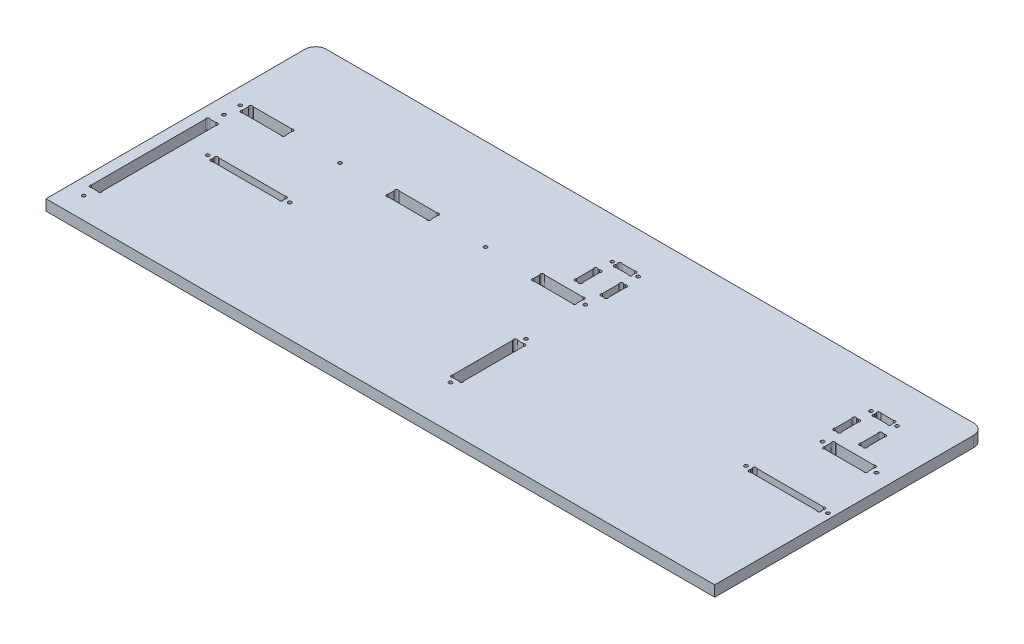
SolidWorks part; units mm, degrees
ref_plane "Plan de face" through (0, 0, 0) normal (0, 0, 1) x (1, 0, 0)
ref_plane "Plan de dessus" through (0, 0, 0) normal (0, 1, 0) x (1, 0, 0)
ref_plane "Plan de droite" through (0, 0, 0) normal (1, 0, 0) x (0, 0, -1)
sketch "Esquisse1" plane through (0, 0, 0) normal (0, 1, 0) x (1, 0, 0)
  line L26 (317, 211.2627) -> (317, 212.7373)
  line L28 (319.2627, 215) -> (330.7373, 215)
  line L29 (333, 211.2627) -> (333, 212.7373)
  line L30 (330.7373, 209) -> (319.2627, 209)
  line L31 (312.2627, 179.5) -> (313.7373, 179.5)
  line L32 (312.2627, 199.5) -> (313.7373, 199.5)
  line L33 (310, 197.2373) -> (310, 181.7627)
  line L34 (316, 181.7627) -> (316, 197.2373)
  line L35 (334, 181.7627) -> (334, 197.2373)
  line L36 (340, 197.2373) -> (340, 181.7627)
  line L37 (337.7373, 199.5) -> (336.2627, 199.5)
  line L38 (337.7373, 179.5) -> (336.2627, 179.5)
  line L39 (552.2627, 179.5) -> (553.7373, 179.5)
  line L40 (552.2627, 199.5) -> (553.7373, 199.5)
  line L41 (550, 197.2373) -> (550, 181.7627)
  line L42 (556, 181.7627) -> (556, 197.2373)
  line L43 (574, 181.7627) -> (574, 197.2373)
  line L44 (580, 197.2373) -> (580, 181.7627)
  line L45 (577.7373, 199.5) -> (576.2627, 199.5)
  line L46 (577.7373, 179.5) -> (576.2627, 179.5)
  line L47 (559.2627, 209) -> (570.7373, 209)
  line L48 (557, 211.2627) -> (557, 212.7373)
  line L49 (570.7373, 215) -> (559.2627, 215)
  line L50 (573, 211.2627) -> (573, 212.7373)
  line L55 (560, 167.7373) -> (560, 162.2627)
  line L56 (600, 167.7373) -> (600, 162.2627)
  line L57 (562.2627, 170) -> (597.7373, 170)
  line L58 (597.7373, 160) -> (562.2627, 160)
  line L59 (292.2627, 160) -> (327.7373, 160)
  line L60 (327.7373, 170) -> (292.2627, 170)
  line L61 (290, 167.7373) -> (290, 162.2627)
  line L62 (330, 167.7373) -> (330, 162.2627)
  line L64 (20, 167.7373) -> (20, 162.2627)
  line L65 (60, 167.7373) -> (60, 162.2627)
  line L66 (22.2627, 170) -> (57.7373, 170)
  line L67 (57.7373, 160) -> (22.2627, 160)
  line L70 (155, 167.7373) -> (155, 162.2627)
  line L71 (195, 167.7373) -> (195, 162.2627)
  line L72 (157.2627, 170) -> (192.7373, 170)
  line L73 (192.7373, 160) -> (157.2627, 160)
  line L76 (10, 250) -> (610, 250)
  line L77 (0, 240) -> (0, 0)
  line L78 (0, 0) -> (620, 0)
  line L79 (620, 240) -> (620, 0)
  line L84 (12.2627, 30) -> (17.7373, 30)
  line L85 (12.2627, 140) -> (17.7373, 140)
  line L86 (10, 137.7373) -> (10, 32.2627)
  line L87 (20, 32.2627) -> (20, 137.7373)
  line L98 (337.7373, 45) -> (332.2627, 45)
  line L99 (337.7373, 105) -> (332.2627, 105)
  line L100 (340, 47.2627) -> (340, 102.7373)
  line L101 (330, 102.7373) -> (330, 47.2627)
  line L109 (610, 109.2627) -> (610, 110.7373)
  line L110 (544, 109.2627) -> (544, 110.7373)
  line L111 (607.7373, 107) -> (546.2627, 107)
  line L112 (546.2627, 113) -> (607.7373, 113)
  line L113 (108.7373, 113) -> (47.2627, 113)
  line L114 (47.2627, 107) -> (108.7373, 107)
  line L115 (111, 109.2627) -> (111, 110.7373)
  line L116 (45, 109.2627) -> (45, 110.7373)
  arc A0 (319.2627, 215) -> (317, 212.7373) centre (318.1314, 213.8686) ccw
  arc A1 (319.2627, 209) -> (317, 211.2627) centre (318.1314, 210.1314) cw
  arc A2 (330.7373, 209) -> (333, 211.2627) centre (331.8686, 210.1314) ccw
  arc A3 (330.7373, 215) -> (333, 212.7373) centre (331.8686, 213.8686) cw
  arc A4 (313.7373, 179.5) -> (316, 181.7627) centre (314.8686, 180.6314) ccw
  arc A5 (312.2627, 179.5) -> (310, 181.7627) centre (311.1314, 180.6314) cw
  arc A6 (312.2627, 199.5) -> (310, 197.2373) centre (311.1314, 198.3686) ccw
  arc A7 (313.7373, 199.5) -> (316, 197.2373) centre (314.8686, 198.3686) cw
  arc A8 (336.2627, 179.5) -> (334, 181.7627) centre (335.1314, 180.6314) cw
  arc A9 (336.2627, 199.5) -> (334, 197.2373) centre (335.1314, 198.3686) ccw
  arc A10 (337.7373, 199.5) -> (340, 197.2373) centre (338.8686, 198.3686) cw
  arc A11 (337.7373, 179.5) -> (340, 181.7627) centre (338.8686, 180.6314) ccw
  arc A12 (552.2627, 179.5) -> (550, 181.7627) centre (551.1314, 180.6314) cw
  arc A13 (552.2627, 199.5) -> (550, 197.2373) centre (551.1314, 198.3686) ccw
  arc A14 (553.7373, 199.5) -> (556, 197.2373) centre (554.8686, 198.3686) cw
  arc A15 (553.7373, 179.5) -> (556, 181.7627) centre (554.8686, 180.6314) ccw
  arc A16 (576.2627, 199.5) -> (574, 197.2373) centre (575.1314, 198.3686) ccw
  arc A17 (577.7373, 199.5) -> (580, 197.2373) centre (578.8686, 198.3686) cw
  arc A18 (577.7373, 179.5) -> (580, 181.7627) centre (578.8686, 180.6314) ccw
  arc A19 (576.2627, 179.5) -> (574, 181.7627) centre (575.1314, 180.6314) cw
  arc A20 (559.2627, 215) -> (557, 212.7373) centre (558.1314, 213.8686) ccw
  arc A21 (559.2627, 209) -> (557, 211.2627) centre (558.1314, 210.1314) cw
  arc A22 (570.7373, 209) -> (573, 211.2627) centre (571.8686, 210.1314) ccw
  arc A23 (570.7373, 215) -> (573, 212.7373) centre (571.8686, 213.8686) cw
  circle A24 centre (313, 212) radius 1.6
  circle A25 centre (337, 212) radius 1.6
  circle A26 centre (553, 212) radius 1.6
  circle A27 centre (577, 212) radius 1.6
  circle A28 centre (555, 165) radius 1.6
  arc A29 (560, 162.2627) -> (562.2627, 160) centre (561.1314, 161.1314) ccw
  arc A30 (560, 167.7373) -> (562.2627, 170) centre (561.1314, 168.8686) cw
  arc A31 (600, 167.7373) -> (597.7373, 170) centre (598.8686, 168.8686) ccw
  arc A32 (600, 162.2627) -> (597.7373, 160) centre (598.8686, 161.1314) cw
  circle A33 centre (605, 165) radius 1.6
  arc A34 (290, 162.2627) -> (292.2627, 160) centre (291.1314, 161.1314) ccw
  arc A35 (290, 167.7373) -> (292.2627, 170) centre (291.1314, 168.8686) cw
  arc A36 (330, 167.7373) -> (327.7373, 170) centre (328.8686, 168.8686) ccw
  arc A37 (330, 162.2627) -> (327.7373, 160) centre (328.8686, 161.1314) cw
  circle A38 centre (335, 165) radius 1.6
  circle A39 centre (15, 165) radius 1.6
  arc A40 (20, 162.2627) -> (22.2627, 160) centre (21.1314, 161.1314) ccw
  arc A41 (20, 167.7373) -> (22.2627, 170) centre (21.1314, 168.8686) cw
  arc A42 (60, 167.7373) -> (57.7373, 170) centre (58.8686, 168.8686) ccw
  arc A43 (60, 162.2627) -> (57.7373, 160) centre (58.8686, 161.1314) cw
  arc A44 (155, 162.2627) -> (157.2627, 160) centre (156.1314, 161.1314) ccw
  arc A45 (155, 167.7373) -> (157.2627, 170) centre (156.1314, 168.8686) cw
  arc A46 (195, 162.2627) -> (192.7373, 160) centre (193.8686, 161.1314) cw
  arc A47 (195, 167.7373) -> (192.7373, 170) centre (193.8686, 168.8686) ccw
  circle A48 centre (242.5, 165) radius 1.6
  circle A49 centre (107.5, 165) radius 1.6
  arc A50 (17.7373, 30) -> (20, 32.2627) centre (18.8686, 31.1314) ccw
  circle A51 centre (15, 20) radius 1.6
  arc A52 (12.2627, 30) -> (10, 32.2627) centre (11.1314, 31.1314) cw
  arc A53 (17.7373, 140) -> (20, 137.7373) centre (18.8686, 138.8686) cw
  arc A54 (12.2627, 140) -> (10, 137.7373) centre (11.1314, 138.8686) ccw
  circle A55 centre (15, 150) radius 1.6
  arc A56 (10, 250) -> (0, 240) centre (10, 240) ccw
  arc A57 (610, 250) -> (620, 240) centre (610, 240) cw
  circle A58 centre (335, 40) radius 1.6
  arc A59 (330, 47.2627) -> (332.2627, 45) centre (331.1314, 46.1314) ccw
  arc A60 (340, 47.2627) -> (337.7373, 45) centre (338.8686, 46.1314) cw
  arc A61 (330, 102.7373) -> (332.2627, 105) centre (331.1314, 103.8686) cw
  arc A62 (340, 102.7373) -> (337.7373, 105) centre (338.8686, 103.8686) ccw
  circle A63 centre (335, 110) radius 1.6
  arc A64 (607.7373, 107) -> (610, 109.2627) centre (608.8686, 108.1314) ccw
  circle A65 centre (615, 110) radius 1.6
  arc A66 (607.7373, 113) -> (610, 110.7373) centre (608.8686, 111.8686) cw
  circle A67 centre (539, 110) radius 1.6
  arc A68 (546.2627, 113) -> (544, 110.7373) centre (545.1314, 111.8686) ccw
  arc A69 (546.2627, 107) -> (544, 109.2627) centre (545.1314, 108.1314) cw
  arc A70 (108.7373, 107) -> (111, 109.2627) centre (109.8686, 108.1314) ccw
  arc A71 (108.7373, 113) -> (111, 110.7373) centre (109.8686, 111.8686) cw
  circle A72 centre (116, 110) radius 1.6
  arc A73 (47.2627, 113) -> (45, 110.7373) centre (46.1314, 111.8686) ccw
  circle A74 centre (40, 110) radius 1.6
  arc A75 (47.2627, 107) -> (45, 109.2627) centre (46.1314, 108.1314) cw
  point P1 (337, 199.5)
  dimension "D25" = 6
  dimension "D28" = 16
  dimension "D29" = 20
  dimension "D32" = 9.5
  dimension "D33" = 35
  dimension "D39" = 10
  dimension "D49" = 1.1314
  dimension "D50" = 40
  dimension "D57" = 6
  dimension "D55" = 76
  dimension "D62" = 3.2
  dimension "D63" = 1.6
  dimension "D64" = 10
  dimension "D65" = 1.1314
  dimension "D66" = 1.1314
  dimension "D67" = 620
  dimension "D9" = 2.2627
  dimension "D10" = 1.6
  dimension "D69" = 3.2
  dimension "D78" = 3.7373
  dimension "D14" = 1.6
  dimension "D36" = 1.6
  dimension "D61" = 1.6
  dimension "D95" = 1.6
  dimension "D107" = 1.6
  dimension "D118" = 1.6
  dimension "D119" = 1.6
  dimension "D128" = 6
  dimension "D141" = 1.6
  dimension "D2" = 250
  dimension "D4" = 5
  dimension "D8" = 20
  dimension "D11" = 5
  dimension "D12" = 5
  dimension "D13" = 40
  dimension "D15" = 5
  dimension "D16" = 1.1314
  dimension "D17" = 1.1314
  dimension "D18" = 5
  dimension "D19" = 2.2627
  dimension "D20" = 2.2627
  dimension "D21" = 80
  dimension "D22" = 10
  dimension "D23" = 1.1314
  dimension "D24" = 1.1314
  dimension "D26" = 6
  dimension "D27" = 6
  dimension "D30" = 40
  dimension "D31" = 18
  dimension "D34" = 4
  dimension "D35" = 4
  dimension "D37" = 1.1314
  dimension "D38" = 2.2627
  dimension "D40" = 1.1314
  dimension "D41" = 1.1314
  dimension "D42" = 1.1314
  dimension "D43" = 1.1314
  dimension "D44" = 3
  dimension "D45" = 1
  dimension "D46" = 1.1314
  dimension "D47" = 1.1314
  dimension "D48" = 1.1314
  dimension "D51" = 3.7373
  dimension "D52" = 66
  dimension "D53" = 10
  dimension "D54" = 66
  dimension "D56" = 107
  dimension "D58" = 3
  dimension "D59" = 1.1314
  dimension "D60" = 2.2627
  dimension "D68" = 60
  dimension "D70" = 6
  dimension "D71" = 3
  dimension "D72" = 1.1314
  dimension "D73" = 1.1314
  dimension "D74" = 63.7373
  dimension "D75" = 2.2627
  dimension "D76" = 2.2627
  dimension "D77" = 45
  dimension "D79" = 45
  dimension "D80" = 5
  dimension "D81" = 5
  dimension "D82" = 5
  dimension "D83" = 280
  dimension "D84" = 1.1314
  dimension "D85" = 1.1314
  dimension "D86" = 1.1314
  dimension "D87" = 1.1314
  dimension "D88" = 10
  dimension "D89" = 110
  dimension "D90" = 30
  dimension "D91" = 10
  dimension "D92" = 5
  dimension "D93" = 10
  dimension "D94" = 10
  dimension "D96" = 1.1314
  dimension "D97" = 1.1314
  dimension "D98" = 1.1314
  dimension "D99" = 92.5
  dimension "D100" = 1.1314
  dimension "D101" = 135
  dimension "D102" = 92.5
  dimension "D103" = 15
  dimension "D104" = 85
  dimension "D105" = 10
  dimension "D106" = 40
  dimension "D108" = 20
  dimension "D109" = 80
  dimension "D110" = 1.1314
  dimension "D111" = 1.1314
  dimension "D112" = 1.1314
  dimension "D113" = 1.1314
  dimension "D114" = 40
  dimension "D115" = 95
  dimension "D116" = 95
  dimension "D117" = 40
  dimension "D120" = 1.1314
  dimension "D121" = 1.1314
  dimension "D122" = 1.1314
  dimension "D123" = 1.1314
  dimension "D124" = 1.1314
  dimension "D125" = 1.1314
  dimension "D126" = 1.1314
  dimension "D127" = 1.1314
  dimension "D129" = 6
  dimension "D130" = 6
  dimension "D131" = 4
  dimension "D132" = 20
  dimension "D133" = 16
  dimension "D134" = 4
  dimension "D135" = 35
  dimension "D136" = 9.5
  dimension "D137" = 283
  dimension "D138" = 3
  dimension "D139" = 1
  dimension "D140" = 18
  dimension "D142" = 1.1314
  dimension "D143" = 1.1314
  dimension "D144" = 1.1314
  dimension "D145" = 1.1314
  dimension "D146" = 1.1314
  dimension "D147" = 1.1314
  dimension "D148" = 1.1314
  dimension "D149" = 1.1314
  dimension "D150" = 1.1314
  dimension "D151" = 1.1314
  dimension "D152" = 1.1314
  dimension "D153" = 1.1314
extrude "Extrusion1" add sketch "Esquisse1" along normal blind 10
